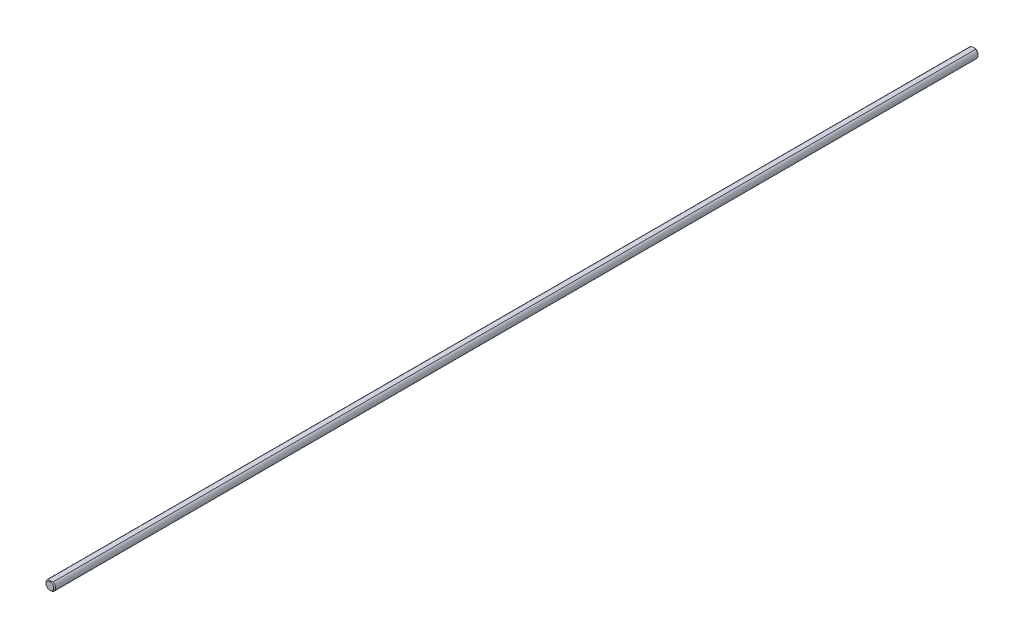
SolidWorks part; units mm, degrees
ref_plane "Front" through (0, 0, 0) normal (0, 0, 1) x (1, 0, 0)
ref_plane "Top" through (0, 0, 0) normal (0, 1, 0) x (1, 0, 0)
ref_plane "Right" through (0, 0, 0) normal (1, 0, 0) x (0, 0, -1)
sketch "Sketch1" plane through (0, 0, 0) normal (0, 0, 1) x (1, 0, 0)
  circle A0 centre (0, 0) radius 3.175
  dimension "D1" = 6.35
extrude "Extrude1" add sketch "Sketch1" along normal mid plane 609.6
chamfer "Chamfer1" distance 0.635 angle 45 2 edges at (3.175, 0, -304.8) (3.175, 0, 304.8)
sketch "Sketch13" plane through (0, 0, 0) normal (0, 0, 1) x (1, 0, 0)
  line L3 (-1.5875, 2.7496) -> (1.5875, 2.7496)
  circle A0 centre (0, 0) radius 3.175 construction
  arc A1 (1.5875, 2.7496) -> (-1.5875, 2.7496) centre (0, 0) ccw
  dimension "D1" = 3.175
extrude "Extrude7" cut sketch "Sketch13" against normal through all and the other way through all
equation "\"D1@Chamfer1\" = \"D1@Sketch1\" * .1"
equation "\"D1@Sketch13\" = \"D1@Sketch1\" * .5"
